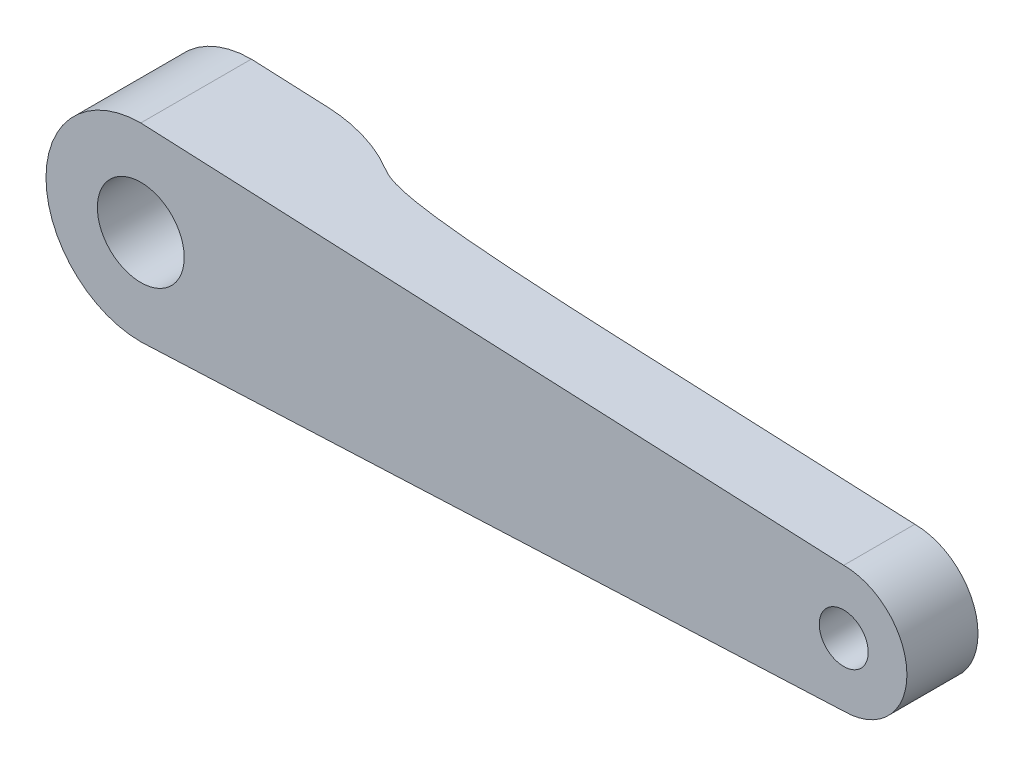
SolidWorks part; units mm, degrees
ref_plane "Ebene vorne" through (0, 0, 0) normal (0, 0, 1) x (1, 0, 0)
ref_plane "Ebene oben" through (0, 0, 0) normal (0, 1, 0) x (1, 0, 0)
ref_plane "Ebene rechts" through (0, 0, 0) normal (1, 0, 0) x (0, 0, -1)
sketch "Sketch1" plane through (0, 0, 0) normal (0, 0, 1) x (1, 0, 0)
  line L0 (0, 0) -> (44.5, 0) construction
  line L1 (0, 6) -> (44.5, 4)
  line L2 (0, -6) -> (44.5, -4)
  circle A1 centre (44.5, 0) radius 1.55
  circle A2 centre (0, 0) radius 6
  circle A3 centre (44.5, 0) radius 4
  dimension "D2" = 12
  dimension "D3" = 3.1
  dimension "D4" = 8
  dimension "D5" = 44.5
extrude "Boss-Extrude1" add sketch "Sketch1" along normal blind 7
sketch "Sketch2" plane through (0, 0, 7) normal (0, 0, 1) x (1, 0, 0)
  circle A0 centre (0, 0) radius 2.75
  dimension "D1" = 5.5
extrude "Cut-Extrude1" cut sketch "Sketch2" against normal blind 5
sketch "Sketch3" plane through (0, 0, 0) normal (0, 0, -1) x (-1, 0, 0)
  circle A0 centre (0, 0) radius 1.75
  dimension "D1" = 3.5
extrude "Cut-Extrude2" cut sketch "Sketch3" against normal blind 5
sketch "Sketch5" plane through (0, 0, 0) normal (0, 1, 0) x (1, 0, 0)
  line L0 (48.5, 0) -> (48.5, -2.5)
  line L1 (48.5, -7) -> (48.5, 0) construction
  line L2 (48.5, -2.5) -> (28.5, -2.5)
  line L3 (-6, 0) -> (9, 0) construction
  line L4 (0, 0) -> (44.5, 0) construction
  line L5 (9, 0) -> (48.5, 0)
  spline S0 degree 3 poles (9, 0) (9.7345, -1.7321) (8.7722, -2.5787) (28.5, -2.5) knots 0 0 0 0 1 1 1 1
  dimension "D1" = 2.5
  dimension "D2" = 20
  dimension "D3" = 15
extrude "Cut-Extrude4" cut sketch "Sketch5" against normal through all and the other way through all
fillet "Fillet1" radius 10 1 edges at (9, 0, 0)
sketch3d "3DSketch1"
  line L0 (0, 0, 7) -> (44.5, 0, 7)
  line L1 (0, 0, 2) -> (0, 0, 7) construction
  line L2 (44.5, 0, 7) -> (44.5, 0, 2.5) construction
  line L3 (44.5, 0, 7) -> (44.5, 0, 2.5) construction
